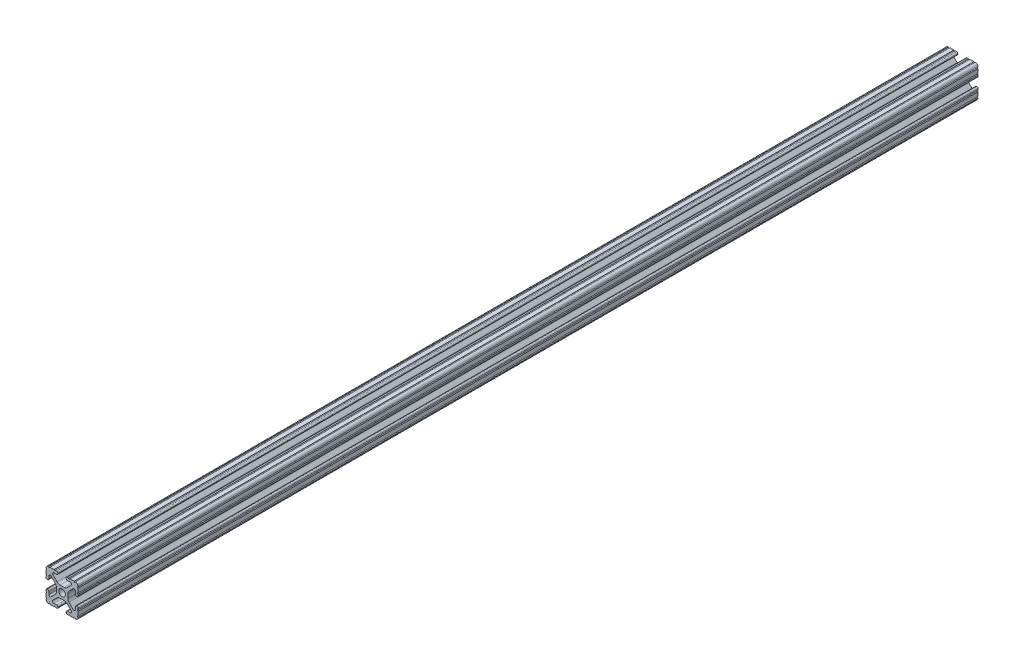
SolidWorks part; units mm, degrees
ref_plane "Front Plane" through (0, 0, 0) normal (0, 0, 1) x (1, 0, 0)
ref_plane "Top Plane" through (0, 0, 0) normal (0, 1, 0) x (1, 0, 0)
ref_plane "Right Plane" through (0, 0, 0) normal (1, 0, 0) x (0, 0, -1)
sketch "Sketch1" plane through (0, 0, 0) normal (0, 0, 1) x (1, 0, 0)
  line L88 (-7.1797, -8.6452) -> (-3.9523, -5.4237)
  line L89 (-1.7093, -4.4958) -> (1.7093, -4.4958)
  line L90 (3.9523, -5.4237) -> (7.1797, -8.6452)
  line L91 (6.4164, -10.4902) -> (4.2875, -10.4902)
  line L92 (3.2385, -11.5392) -> (3.2385, -11.651)
  line L93 (4.2875, -12.7) -> (5.3171, -12.7)
  line L94 (6.3331, -12.7) -> (9.5504, -12.7)
  line L95 (12.7, -9.5504) -> (12.7, -6.3331)
  line L96 (12.7, -5.3171) -> (12.7, -4.2875)
  line L97 (11.651, -3.2385) -> (11.5392, -3.2385)
  line L98 (10.4902, -4.2875) -> (10.4902, -6.4021)
  line L99 (8.7371, -7.1294) -> (5.441, -3.8408)
  line L100 (4.5085, -1.5932) -> (4.5085, 1.5932)
  line L101 (5.441, 3.8408) -> (8.7371, 7.1294)
  line L102 (10.4902, 6.4021) -> (10.4902, 4.2875)
  line L103 (11.5392, 3.2385) -> (11.651, 3.2385)
  line L104 (12.7, 4.2875) -> (12.7, 5.3171)
  line L105 (12.7, 6.3331) -> (12.7, 9.5504)
  line L106 (9.5504, 12.7) -> (6.3331, 12.7)
  line L107 (5.3171, 12.7) -> (4.2875, 12.7)
  line L108 (3.2385, 11.651) -> (3.2385, 11.5392)
  line L109 (4.2875, 10.4902) -> (6.4768, 10.4902)
  line L110 (7.207, 8.7244) -> (3.8983, 5.4232)
  line L111 (1.6558, 4.4958) -> (-1.6558, 4.4958)
  line L112 (-3.8983, 5.4232) -> (-7.207, 8.7244)
  line L113 (-6.4768, 10.4902) -> (-4.2875, 10.4902)
  line L114 (-3.2385, 11.5392) -> (-3.2385, 11.651)
  line L115 (-4.2875, 12.7) -> (-5.3171, 12.7)
  line L116 (-6.3331, 12.7) -> (-9.5504, 12.7)
  line L117 (-12.7, 9.5504) -> (-12.7, 6.3331)
  line L118 (-12.7, 5.3171) -> (-12.7, 4.2875)
  line L119 (-11.651, 3.2385) -> (-11.5392, 3.2385)
  line L120 (-10.4902, 4.2875) -> (-10.4902, 6.4021)
  line L121 (-8.7371, 7.1294) -> (-5.441, 3.8408)
  line L122 (-4.5085, 1.5932) -> (-4.5085, -1.5932)
  line L123 (-5.441, -3.8408) -> (-8.7371, -7.1294)
  line L124 (-10.4902, -6.4021) -> (-10.4902, -4.2875)
  line L125 (-11.5392, -3.2385) -> (-11.651, -3.2385)
  line L126 (-12.7, -4.2875) -> (-12.7, -5.3171)
  line L127 (-12.7, -6.3331) -> (-12.7, -9.5504)
  line L128 (-9.5504, -12.7) -> (-6.3331, -12.7)
  line L129 (-5.3171, -12.7) -> (-4.2875, -12.7)
  line L130 (-3.2385, -11.651) -> (-3.2385, -11.5392)
  line L131 (-4.2875, -10.4902) -> (-6.4164, -10.4902)
  circle A1 centre (0, 0) radius 2.6035
  arc A104 (-7.1797, -8.6452) -> (-6.4164, -10.4902) centre (-6.4164, -9.4098) ccw
  arc A105 (-1.7093, -4.4958) -> (-3.9523, -5.4237) centre (-1.7093, -7.6708) ccw
  arc A106 (3.9523, -5.4237) -> (1.7093, -4.4958) centre (1.7093, -7.6708) ccw
  arc A107 (6.4164, -10.4902) -> (7.1797, -8.6452) centre (6.4164, -9.4098) ccw
  arc A108 (4.2875, -10.4902) -> (3.2385, -11.5392) centre (4.2875, -11.5392) ccw
  arc A109 (3.2385, -11.651) -> (4.2875, -12.7) centre (4.2875, -11.651) ccw
  arc A110 (6.3331, -12.7) -> (5.3171, -12.7) centre (5.8251, -12.7) ccw
  arc A111 (10.5664, -12.6998) -> (9.5504, -12.7) centre (10.0584, -12.7) ccw
  arc A112 (10.5664, -12.6998) -> (12.6998, -10.5664) centre (10.5918, -10.5918) ccw
  arc A113 (12.7, -9.5504) -> (12.6998, -10.5664) centre (12.7, -10.0584) ccw
  arc A114 (12.7, -5.3171) -> (12.7, -6.3331) centre (12.7, -5.8251) ccw
  arc A115 (12.7, -4.2875) -> (11.651, -3.2385) centre (11.651, -4.2875) ccw
  arc A116 (11.5392, -3.2385) -> (10.4902, -4.2875) centre (11.5392, -4.2875) ccw
  arc A117 (8.7371, -7.1294) -> (10.4902, -6.4021) centre (9.4628, -6.4021) ccw
  arc A118 (4.5085, -1.5932) -> (5.441, -3.8408) centre (7.6835, -1.5932) ccw
  arc A119 (5.441, 3.8408) -> (4.5085, 1.5932) centre (7.6835, 1.5932) ccw
  arc A120 (10.4902, 6.4021) -> (8.7371, 7.1294) centre (9.4628, 6.4021) ccw
  arc A121 (10.4902, 4.2875) -> (11.5392, 3.2385) centre (11.5392, 4.2875) ccw
  arc A122 (11.651, 3.2385) -> (12.7, 4.2875) centre (11.651, 4.2875) ccw
  arc A123 (12.7, 6.3331) -> (12.7, 5.3171) centre (12.7, 5.8251) ccw
  arc A124 (12.6998, 10.5664) -> (12.7, 9.5504) centre (12.7, 10.0584) ccw
  arc A125 (12.6998, 10.5664) -> (10.5664, 12.6998) centre (10.5918, 10.5918) ccw
  arc A126 (9.5504, 12.7) -> (10.5664, 12.6998) centre (10.0584, 12.7) ccw
  arc A127 (5.3171, 12.7) -> (6.3331, 12.7) centre (5.8251, 12.7) ccw
  arc A128 (4.2875, 12.7) -> (3.2385, 11.651) centre (4.2875, 11.651) ccw
  arc A129 (3.2385, 11.5392) -> (4.2875, 10.4902) centre (4.2875, 11.5392) ccw
  arc A130 (7.207, 8.7244) -> (6.4768, 10.4902) centre (6.4768, 9.4563) ccw
  arc A131 (1.6558, 4.4958) -> (3.8983, 5.4232) centre (1.6558, 7.6708) ccw
  arc A132 (-3.8983, 5.4232) -> (-1.6558, 4.4958) centre (-1.6558, 7.6708) ccw
  arc A133 (-6.4768, 10.4902) -> (-7.207, 8.7244) centre (-6.4768, 9.4563) ccw
  arc A134 (-4.2875, 10.4902) -> (-3.2385, 11.5392) centre (-4.2875, 11.5392) ccw
  arc A135 (-3.2385, 11.651) -> (-4.2875, 12.7) centre (-4.2875, 11.651) ccw
  arc A136 (-6.3331, 12.7) -> (-5.3171, 12.7) centre (-5.8251, 12.7) ccw
  arc A137 (-10.5664, 12.6998) -> (-9.5504, 12.7) centre (-10.0584, 12.7) ccw
  arc A138 (-10.5664, 12.6998) -> (-12.6998, 10.5664) centre (-10.5918, 10.5918) ccw
  arc A139 (-12.7, 9.5504) -> (-12.6998, 10.5664) centre (-12.7, 10.0584) ccw
  arc A140 (-12.7, 5.3171) -> (-12.7, 6.3331) centre (-12.7, 5.8251) ccw
  arc A141 (-12.7, 4.2875) -> (-11.651, 3.2385) centre (-11.651, 4.2875) ccw
  arc A142 (-11.5392, 3.2385) -> (-10.4902, 4.2875) centre (-11.5392, 4.2875) ccw
  arc A143 (-8.7371, 7.1294) -> (-10.4902, 6.4021) centre (-9.4628, 6.4021) ccw
  arc A144 (-4.5085, 1.5932) -> (-5.441, 3.8408) centre (-7.6835, 1.5932) ccw
  arc A145 (-5.441, -3.8408) -> (-4.5085, -1.5932) centre (-7.6835, -1.5932) ccw
  arc A146 (-10.4902, -6.4021) -> (-8.7371, -7.1294) centre (-9.4628, -6.4021) ccw
  arc A147 (-10.4902, -4.2875) -> (-11.5392, -3.2385) centre (-11.5392, -4.2875) ccw
  arc A148 (-11.651, -3.2385) -> (-12.7, -4.2875) centre (-11.651, -4.2875) ccw
  arc A149 (-12.7, -6.3331) -> (-12.7, -5.3171) centre (-12.7, -5.8251) ccw
  arc A150 (-12.6998, -10.5664) -> (-12.7, -9.5504) centre (-12.7, -10.0584) ccw
  arc A151 (-12.6998, -10.5664) -> (-10.5664, -12.6998) centre (-10.5918, -10.5918) ccw
  arc A152 (-9.5504, -12.7) -> (-10.5664, -12.6998) centre (-10.0584, -12.7) ccw
  arc A153 (-5.3171, -12.7) -> (-6.3331, -12.7) centre (-5.8251, -12.7) ccw
  arc A154 (-4.2875, -12.7) -> (-3.2385, -11.651) centre (-4.2875, -11.651) ccw
  arc A155 (-3.2385, -11.5392) -> (-4.2875, -10.4902) centre (-4.2875, -11.5392) ccw
extrude "Boss-Extrude1" add sketch "Sketch1" along normal mid plane 711.2
